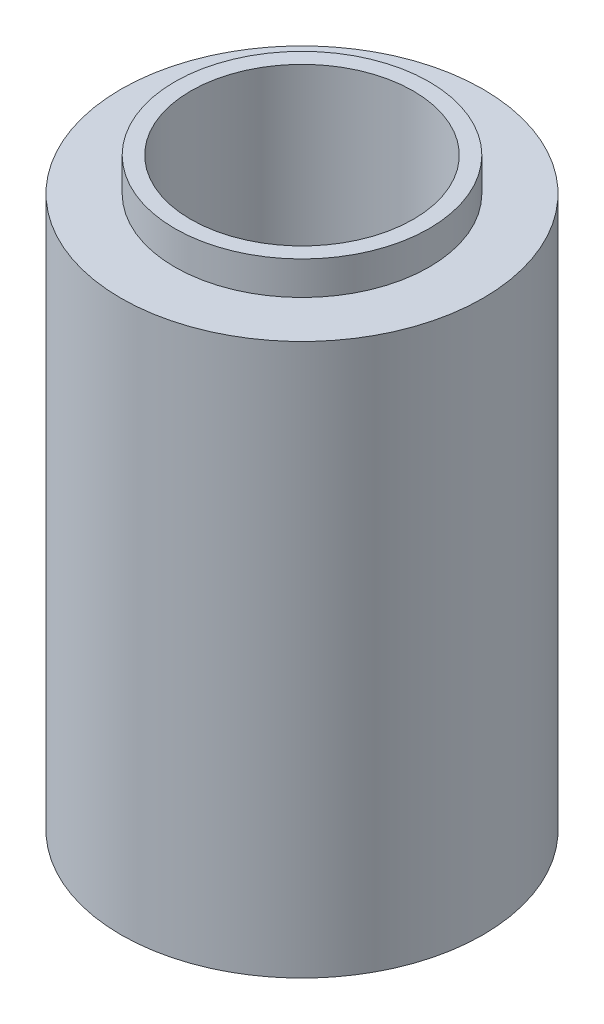
SolidWorks part; units mm, degrees
ref_plane "Front Plane" through (0, 0, 0) normal (0, 0, 1) x (1, 0, 0)
ref_plane "Top Plane" through (0, 0, 0) normal (0, 1, 0) x (1, 0, 0)
ref_plane "Right Plane" through (0, 0, 0) normal (1, 0, 0) x (0, 0, -1)
sketch "Sketch1" plane through (0, 0, 0) normal (0, 1, 0) x (1, 0, 0)
  circle A0 centre (0, 0) radius 17.9
  dimension "D1" = 35.8
extrude "Boss-Extrude1" add sketch "Sketch1" along normal blind 54.51
sketch "Sketch2" plane through (0, 54.51, 0) normal (0, 1, 0) x (1, 0, 0)
  circle A0 centre (0, 0) radius 12.5735
extrude "Boss-Extrude2" add sketch "Sketch2" along normal blind 3.3
sketch "Sketch3" plane through (0, 57.81, 0) normal (0, 1, 0) x (1, 0, 0)
  circle A0 centre (0, 0) radius 15.25
sketch "Sketch4" plane through (0, 0, 0) normal (0, -1, 0) x (1, 0, 0)
  circle A0 centre (0, 0) radius 11
  dimension "D1" = 22
extrude "Cut-Extrude2" cut sketch "Sketch4" against normal blind 59.3
